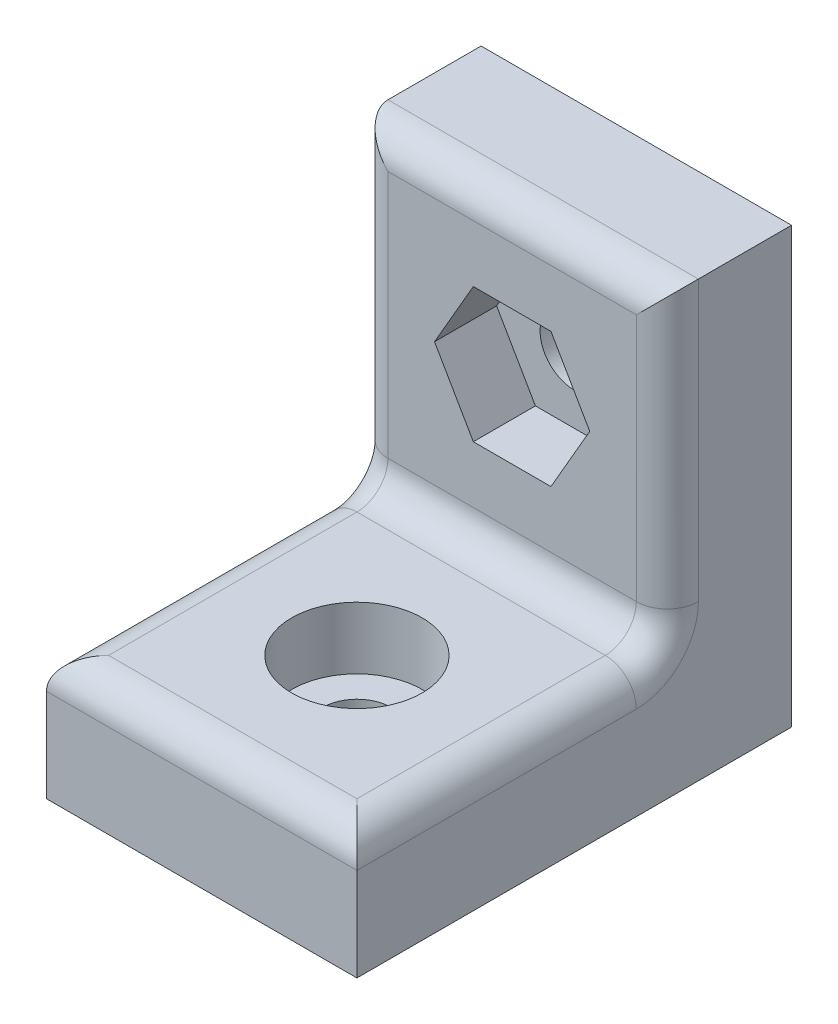
SolidWorks part; units mm, degrees
ref_plane "Plan de face" through (0, 0, 0) normal (0, 0, 1) x (1, 0, 0)
ref_plane "Plan de dessus" through (0, 0, 0) normal (0, 1, 0) x (1, 0, 0)
ref_plane "Plan de droite" through (0, 0, 0) normal (1, 0, 0) x (0, 0, -1)
sketch "Esquisse1" plane through (0, 0, 0) normal (0, 0, 1) x (1, 0, 0)
  line L1 (-5, 14) -> (5, 14)
  line L2 (-5, 14) -> (-5, 0)
  line L3 (-5, 0) -> (5, 0)
  line L4 (5, 14) -> (5, 0)
  dimension "D1" = 10
  dimension "D2" = 14
  dimension "D3" = 5
extrude "Boss.-Extru.1" add sketch "Esquisse1" along normal blind 4
sketch "Esquisse2" plane through (0, 0, 4) normal (0, 0, 1) x (1, 0, 0)
  line L0 (5, 0) -> (5, 14) construction
  line L1 (-5, 0) -> (5, 0)
  line L2 (-5, 0) -> (-5, 4)
  line L3 (-5, 4) -> (5, 4)
  line L4 (5, 0) -> (5, 4)
  dimension "D1" = 4
extrude "Boss.-Extru.2" add sketch "Esquisse2" along normal blind 10
sketch "Esquisse3" plane through (0, 0, 4) normal (0, 0, 1) x (1, 0, 0)
  line L0 (5, 14) -> (-5, 14) construction
  line L1 (-5, 14) -> (-5, 4) construction
  circle A0 centre (0, 9) radius 1.1
  point P2 (0, 14)
  point P3 (-5, 9)
  dimension "D1" = 2.2
extrude "Enlèv. mat.-Extru.1" cut sketch "Esquisse3" against normal through all
fillet "Congé1" radius 1 7 edges at (0, 4, 4) (5, 9, 4) (-5, 9, 4) (0, 14, 4) (0, 4, 14) (5, 4, 9) (-5, 4, 9)
sketch "Esquisse4" plane through (0, 4, 0) normal (0, 1, 0) x (1, 0, 0)
  line L0 (5, -14) -> (-5, -14) construction
  line L1 (-5, -14) -> (-5, -4) construction
  circle A0 centre (0, -9) radius 1.1
  point P0 (0, -14)
  point P1 (-5, -9)
  dimension "D1" = 2.2
extrude "Enlèv. mat.-Extru.2" cut sketch "Esquisse4" against normal through all
sketch "Esquisse5" plane through (0, 0, 4) normal (0, 0, 1) x (1, 0, 0)
  line L0 (5, 14) -> (-5, 14) construction
  line L1 (1.25, 6.8349) -> (2.5, 9)
  line L2 (2.5, 9) -> (1.25, 11.1651)
  line L3 (1.25, 11.1651) -> (-1.25, 11.1651)
  line L4 (-1.25, 11.1651) -> (-2.5, 9)
  line L5 (-2.5, 9) -> (-1.25, 6.8349)
  line L6 (-1.25, 6.8349) -> (1.25, 6.8349)
  circle A1 centre (0, 9) radius 2.1651 construction
  dimension "D1" = 2.5
extrude "Enlèv. mat.-Extru.3" cut sketch "Esquisse5" against normal blind 2
sketch "Esquisse6" plane through (0, 4, 0) normal (0, 1, 0) x (1, 0, 0)
  circle A0 centre (0, -9) radius 2.1
  dimension "D1" = 4.2
extrude "Enlèv. mat.-Extru.4" cut sketch "Esquisse6" against normal blind 2
